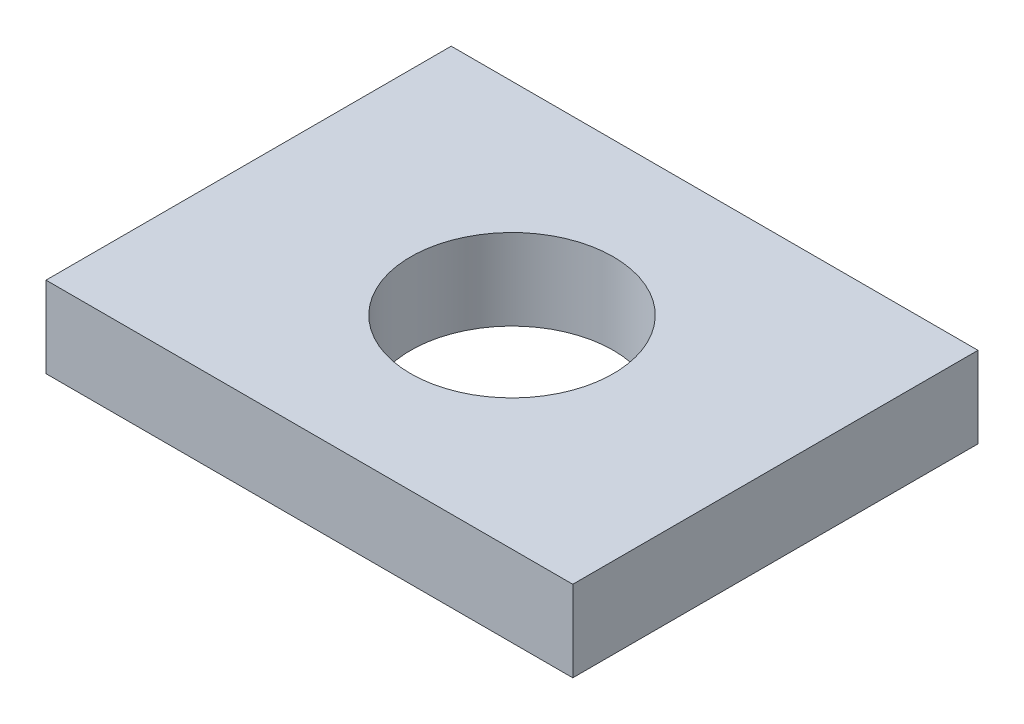
SolidWorks part; units mm, degrees
ref_plane "Alzado" through (0, 0, 0) normal (0, 0, 1) x (1, 0, 0)
ref_plane "Planta" through (0, 0, 0) normal (0, 1, 0) x (1, 0, 0)
ref_plane "Vista lateral" through (0, 0, 0) normal (1, 0, 0) x (0, 0, -1)
sketch "Croquis1" plane through (0, 0, 0) normal (0, 1, 0) x (1, 0, 0)
  line L1 (-6.5, -5) -> (6.5, -5)
  line L2 (-6.5, -5) -> (-6.5, 5)
  line L3 (-6.5, 5) -> (6.5, 5)
  line L4 (6.5, -5) -> (6.5, 5)
  line L5 (-6.5, -5) -> (6.5, 5) construction
  line L6 (-6.5, 5) -> (6.5, -5) construction
  circle A0 centre (0, 0) radius 2.5
  point P0 (0, 0)
  dimension "D1" = 10
  dimension "D2" = 13
extrude "Saliente-Extruir1" add sketch "Croquis1" along normal blind 2
